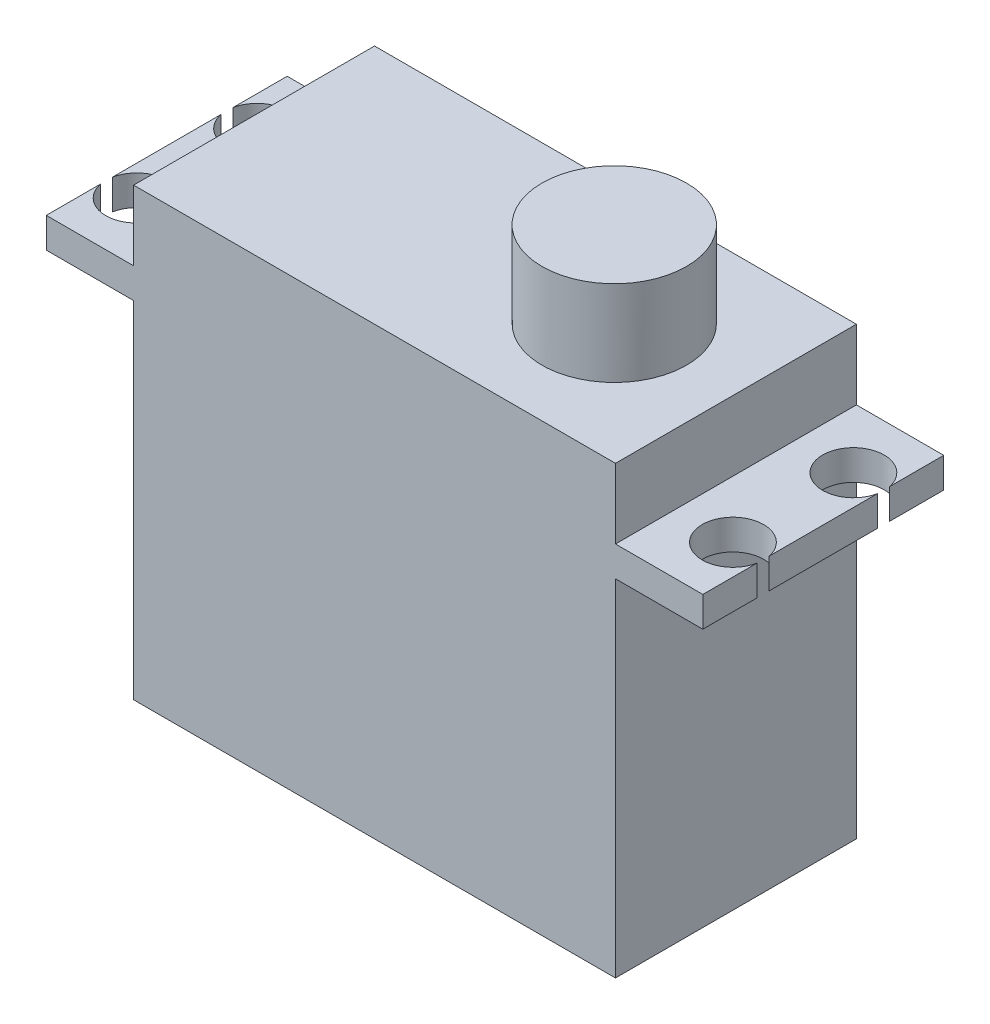
SolidWorks part; units mm, degrees
ref_plane "Front Plane" through (0, 0, 0) normal (0, 0, 1) x (1, 0, 0)
ref_plane "Top Plane" through (0, 0, 0) normal (0, 1, 0) x (1, 0, 0)
ref_plane "Right Plane" through (0, 0, 0) normal (1, 0, 0) x (0, 0, -1)
sketch "Sketch1" plane through (0, 0, 0) normal (0, 1, 0) x (1, 0, 0)
  line L1 (-20, -10) -> (20, -10)
  line L2 (-20, -10) -> (-20, 10)
  line L3 (-20, 10) -> (20, 10)
  line L4 (20, -10) -> (20, 10)
  line L5 (-20, -10) -> (20, 10) construction
  line L6 (-20, 10) -> (20, -10) construction
  point P0 (0, 0)
  dimension "D1" = 40
  dimension "D2" = 20
extrude "Boss-Extrude1" add sketch "Sketch1" along normal blind 28.7
sketch "Sketch2" plane through (0, 28.7, 0) normal (0, 1, 0) x (1, 0, 0)
  line L1 (-27.25, -10) -> (27.25, -10)
  line L2 (-27.25, -10) -> (-27.25, 10)
  line L3 (-27.25, 10) -> (27.25, 10)
  line L4 (27.25, -10) -> (27.25, 10)
  line L5 (-27.25, -10) -> (27.25, 10) construction
  line L6 (-27.25, 10) -> (27.25, -10) construction
  point P0 (0, 0)
  dimension "D1" = 54.5
  dimension "D2" = 20
extrude "Boss-Extrude2" add sketch "Sketch2" along normal blind 2.5
sketch "Sketch3" plane through (0, 31.2, 0) normal (0, 1, 0) x (1, 0, 0)
  line L0 (27.25, 10) -> (-27.25, 10) construction
  line L1 (-20, -10) -> (20, -10)
  line L2 (-20, -10) -> (-20, 10)
  line L3 (-20, 10) -> (20, 10)
  line L4 (20, -10) -> (20, 10)
  line L5 (-20, -10) -> (20, 10) construction
  line L6 (-20, 10) -> (20, -10) construction
  point P0 (0, 0)
  dimension "D1" = 40
extrude "Boss-Extrude3" add sketch "Sketch3" along normal blind 5.8
sketch "Sketch4" plane through (0, 37, 0) normal (0, 1, 0) x (1, 0, 0)
  line L0 (-20, 0) -> (9.9, 0) construction
  line L1 (-20, 10) -> (-20, -10) construction
  circle A0 centre (9.9, 0) radius 6
  dimension "D2" = 12
  dimension "D1" = 29.9
extrude "Boss-Extrude4" add sketch "Sketch4" along normal blind 7.1
ref_plane "Plane1" through (0, 31.2, 0) normal (0, 1, 0) x (1, 0, 0)
sketch "Sketch5" plane through (0, 31.2, 0) normal (0, 1, 0) x (1, 0, 0)
  line L0 (0, 0) -> (-24.75, 0) construction
  line L1 (-24.75, 0) -> (-24.75, 5) construction
  line L2 (0, 0) -> (0, 10) construction
  line L3 (20, 10) -> (-20, 10) construction
  circle A0 centre (-24.75, 5) radius 2.55
  circle A1 centre (-24.75, -5) radius 2.55
  circle A2 centre (24.75, -5) radius 2.55
  circle A3 centre (24.75, 5) radius 2.55
  dimension "D1" = 5.1
  dimension "D2" = 24.75
  dimension "D3" = 5
extrude "Cut-Extrude3" cut sketch "Sketch5" against normal blind 7.1
